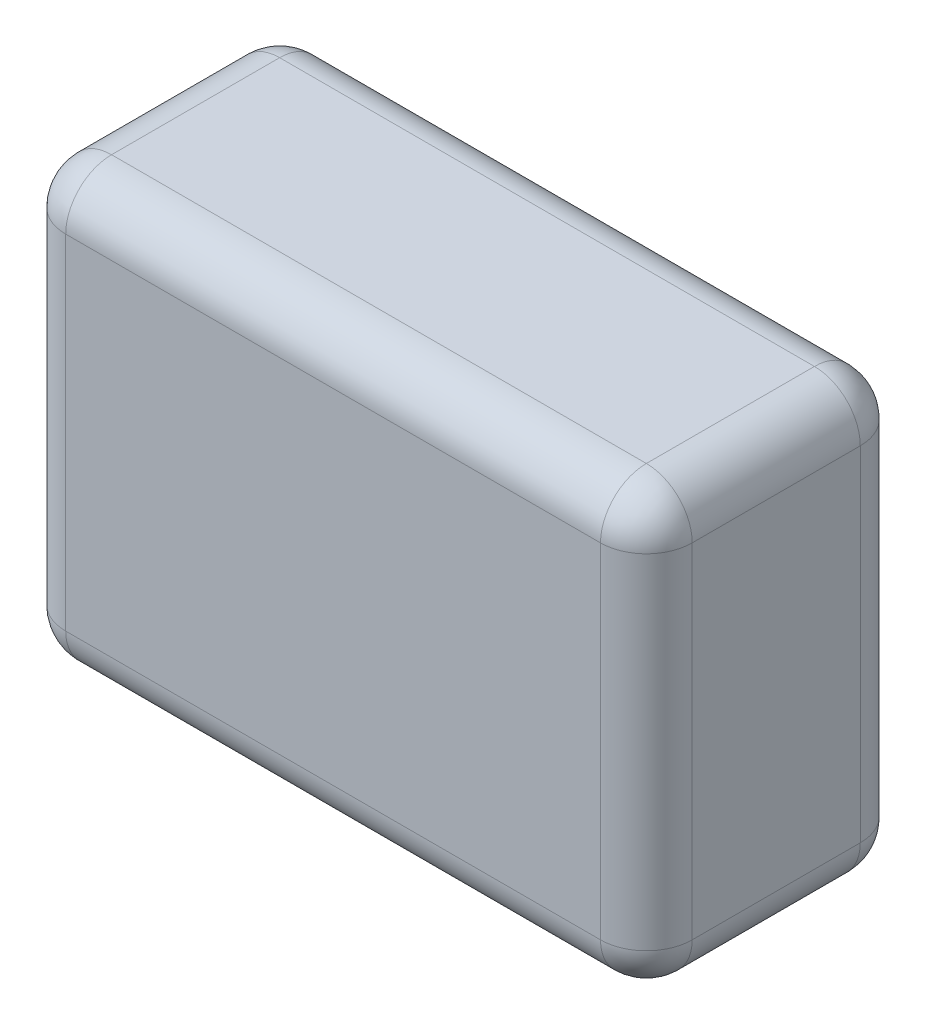
SolidWorks part; units mm, degrees
ref_plane "Front Plane" through (0, 0, 0) normal (0, 0, 1) x (1, 0, 0)
ref_plane "Top Plane" through (0, 0, 0) normal (0, 1, 0) x (1, 0, 0)
ref_plane "Right Plane" through (0, 0, 0) normal (1, 0, 0) x (0, 0, -1)
sketch "Sketch1" plane through (0, 0, 0) normal (0, 1, 0) x (1, 0, 0)
  line L0 (-41, -17) -> (41, 17) construction
  line L1 (-41, 17) -> (41, 17)
  line L2 (-41, 17) -> (-41, -17)
  line L3 (-41, -17) -> (41, -17)
  line L4 (41, 17) -> (41, -17)
  dimension "D1" = 82
  dimension "D2" = 34
extrude "Boss-Extrude1" add sketch "Sketch1" along normal mid plane 57
fillet "Fillet1" radius 6 12 edges at (-41, 0, 17) (41, 0, 17) (41, 0, -17) (-41, 0, -17) (0, 28.5, -17) (41, 28.5, 0) (0, 28.5, 17) (-41, 28.5, 0) (0, -28.5, -17) (41, -28.5, 0) (0, -28.5, 17) (-41, -28.5, 0)
